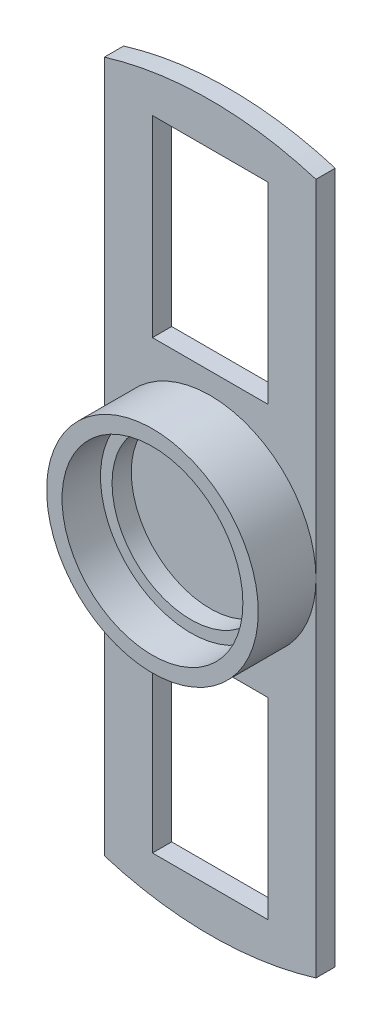
SolidWorks part; units mm, degrees
ref_plane "Front Plane" through (0, 0, 0) normal (0, 0, 1) x (1, 0, 0)
ref_plane "Top Plane" through (0, 0, 0) normal (0, 1, 0) x (1, 0, 0)
ref_plane "Right Plane" through (0, 0, 0) normal (1, 0, 0) x (0, 0, -1)
sketch "Sketch1" plane through (0, 0, 0) normal (0, 0, 1) x (1, 0, 0)
  circle A0 centre (0, 0) radius 23.5
  circle A1 centre (0, 0) radius 27.5
  dimension "D1" = 47
  dimension "D2" = 4
extrude "Boss-Extrude1" add sketch "Sketch1" along normal blind 10
sketch "Sketch2" plane through (0, 0, 0) normal (0, 0, -1) x (-1, 0, 0)
  circle A0 centre (0, 0) radius 27.5
  circle A1 centre (0, 0) radius 20.5
  circle A2 centre (0, 0) radius 23.5 construction
  dimension "D1" = 3
extrude "Boss-Extrude2" add sketch "Sketch2" along normal blind 5
sketch "Sketch3" plane through (0, 0, -5) normal (0, 0, -1) x (-1, 0, 0)
  line L2 (-27.5, 89.8874) -> (-27.5, -89.8874)
  line L4 (27.5, 89.8874) -> (27.5, -89.8874)
  arc A0 (27.5, 89.8874) -> (-27.5, 89.8874) centre (0, 0) ccw
  circle A1 centre (0, 0) radius 27.5 construction
  arc A3 (-27.5, -89.8874) -> (27.5, -89.8874) centre (0, 0) ccw
  point P7 (0, 0)
  point P8 (30.8814, 88.7825)
  point P9 (-27.5, 0)
  dimension "D1" = 188
extrude "Boss-Extrude3" add sketch "Sketch3" along normal blind 5
sketch "Sketch4" plane through (0, 0, -5) normal (0, 0, 1) x (1, 0, 0)
  line L1 (15, -33) -> (-15, -33)
  line L2 (15, -33) -> (15, -83)
  line L3 (15, -83) -> (-15, -83)
  line L4 (-15, -33) -> (-15, -83)
  line L5 (-15, 33) -> (15, 33)
  line L6 (-15, 33) -> (-15, 83)
  line L7 (-15, 83) -> (15, 83)
  line L8 (15, 33) -> (15, 83)
  point P8 (0, -83)
  point P10 (0, 33)
  dimension "D1" = 30
  dimension "D2" = 50
  dimension "D3" = 50
  dimension "D4" = 33
  dimension "D5" = 33
extrude "Cut-Extrude1" cut sketch "Sketch4" against normal blind 10
